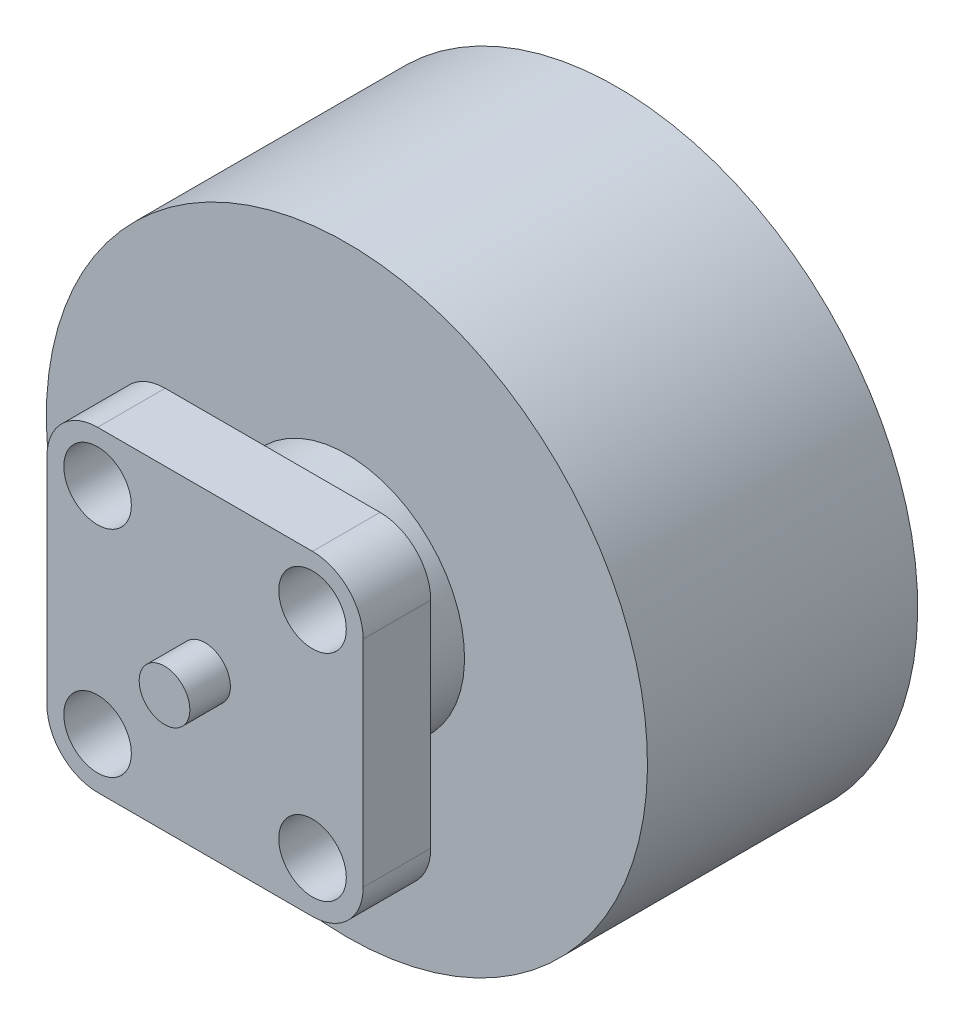
SolidWorks part; units mm, degrees
ref_plane "Front Plane" through (0, 0, 0) normal (0, 0, 1) x (1, 0, 0)
ref_plane "Top Plane" through (0, 0, 0) normal (0, 1, 0) x (1, 0, 0)
ref_plane "Right Plane" through (0, 0, 0) normal (1, 0, 0) x (0, 0, -1)
sketch "Sketch1" plane through (0, 0, 0) normal (1, 0, 0) x (0, 0, -1)
  line L0 (-1.2, 0) -> (16.4, 0)
  line L2 (-1.2, 0.75) -> (16.4, 0.75)
  line L3 (-1.2, 0.75) -> (-1.2, -0.75)
  line L4 (-1.2, -0.75) -> (16.4, -0.75)
  line L5 (16.4, 0.75) -> (16.4, -0.75)
  line L6 (4.2, 0) -> (12.2, 0)
  line L7 (4.2, 0) -> (4.2, 8.9)
  line L8 (4.2, 8.9) -> (12.2, 8.9)
  line L9 (12.2, 0) -> (12.2, 8.9)
  line L10 (0, 0) -> (4.2, 0)
  line L11 (0, 0) -> (0, 3.4836)
  line L12 (0, 3.4836) -> (4.2, 3.4836)
  line L13 (4.2, 0) -> (4.2, 3.4836)
  dimension "D1" = 17.6
  dimension "D2" = 1.5
  dimension "D3" = 1.2
  dimension "D4" = 4.2
  dimension "D5" = 8
  dimension "D6" = 8.9
revolve "Revolve1" add sketch "Sketch1" angle 360 about L0
sketch "Sketch2" plane through (0, 0, 0) normal (0, 0, 1) x (1, 0, 0)
  line L1 (0, 0) -> (4.5, 0) construction
  line L3 (-4.682, -4.682) -> (4.682, -4.682)
  line L4 (-4.682, -4.682) -> (-4.682, 4.682)
  line L5 (-4.682, 4.682) -> (4.682, 4.682)
  line L6 (4.682, -4.682) -> (4.682, 4.682)
  line L7 (-4.682, -4.682) -> (4.682, 4.682) construction
  line L8 (-4.682, 4.682) -> (4.682, -4.682) construction
  circle A0 centre (3.182, 3.182) radius 1
  circle A1 centre (0, 0) radius 4.5 construction
  circle A2 centre (3.182, -3.182) radius 1
  circle A3 centre (-3.182, -3.182) radius 1
  circle A4 centre (-3.182, 3.182) radius 1
  point P15 (0, 0)
  dimension "D1" = 2
  dimension "D2" = 9
  dimension "D3" = 1.5
  dimension "D4" = 4
extrude "Boss-Extrude1" add sketch "Sketch2" against normal blind 2
fillet "Fillet1" radius 1.5 4 edges at (4.682, -4.682, -1) (-4.682, -4.682, -1) (-4.682, 4.682, -1) (4.682, 4.682, -1)
sketch "Sketch3" plane through (0, 0, -12.2) normal (0, 0, -1) x (-1, 0, 0)
  circle A0 centre (0, 2.5) radius 1
  circle A1 centre (0, 0) radius 2.5 construction
  circle A2 centre (2.5, 0) radius 1
  circle A3 centre (0, -2.5) radius 1
  circle A4 centre (-2.5, 0) radius 1
  point P13 (0, 0)
  dimension "D1" = 2
  dimension "D2" = 5
  dimension "D3" = 4
extrude "Cut-Extrude1" cut sketch "Sketch3" against normal blind 2
